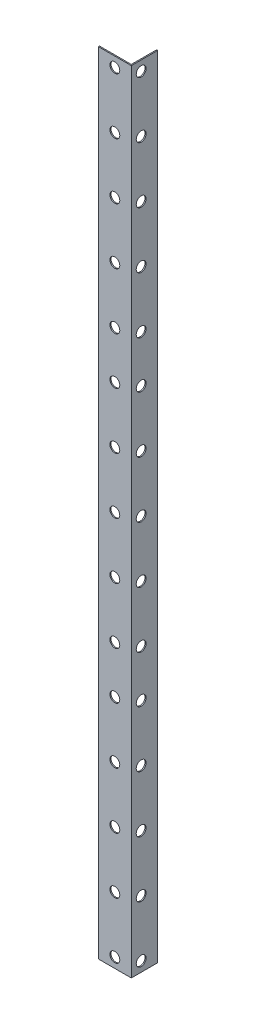
SolidWorks part; units mm, degrees
material "6061-T6 (SS)"
ref_plane "Alzado" through (0, 0, 0) normal (0, 0, 1) x (1, 0, 0)
ref_plane "Planta" through (0, 0, 0) normal (0, 1, 0) x (1, 0, 0)
ref_plane "Vista lateral" through (0, 0, 0) normal (1, 0, 0) x (0, 0, -1)
sketch "Sketch1" plane through (0, 0, 0) normal (0, 1, 0) x (1, 0, 0)
  line L0 (0, 0) -> (15, 0)
  line L1 (15, 0) -> (15, 12)
  line L2 (15, 12) -> (14.5, 12)
  line L3 (14.5, 12) -> (14.5, 0.5)
  line L4 (14.5, 0.5) -> (0, 0.5)
  line L5 (0, 0.5) -> (0, 0)
  dimension "D1" = 15
  dimension "D2" = 12
  dimension "D3" = 0.5
  dimension "D4" = 0.5
extrude "Boss-Extrude1" add sketch "Sketch1" along normal blind 360
sketch "Sketch2" plane through (14.5, 0, 0) normal (-1, 0, 0) x (0, 0, 1)
  circle A0 centre (-4.5, 355.5) radius 2.25
  circle A1 centre (-4.5, 329.8125) radius 2.25
  circle A2 centre (-4.5, 304.125) radius 2.25
  circle A3 centre (-4.5, 278.4375) radius 2.25
  circle A4 centre (-4.5, 252.75) radius 2.25
  circle A5 centre (-4.5, 231.375) radius 2.25
  circle A6 centre (-4.5, 205.6875) radius 2.25
  circle A7 centre (-4.5, 180) radius 2.25
  circle A8 centre (-4.5, 154.3125) radius 2.25
  circle A9 centre (-4.5, 128.625) radius 2.25
  circle A10 centre (-4.5, 107.25) radius 2.25
  circle A11 centre (-4.5, 81.5625) radius 2.25
  circle A12 centre (-4.5, 55.875) radius 2.25
  circle A13 centre (-4.5, 30.1875) radius 2.25
  circle A14 centre (-4.5, 4.5) radius 2.25
  dimension "D1" = 4.5
extrude "Cut-Extrude1" cut sketch "Sketch2" against normal up to next
sketch "Sketch3" plane through (0, 0, 0) normal (0, 0, 1) x (1, 0, 0)
  circle A0 centre (7.5, 355.5) radius 2.25
  circle A1 centre (7.5, 329.8437) radius 2.25
  circle A2 centre (7.5, 304.1875) radius 2.25
  circle A3 centre (7.5, 278.5312) radius 2.25
  circle A4 centre (7.5, 252.875) radius 2.25
  circle A5 centre (7.5, 231.3125) radius 2.25
  circle A6 centre (7.5, 205.6562) radius 2.25
  circle A7 centre (7.5, 180) radius 2.25
  circle A8 centre (7.5, 154.3437) radius 2.25
  circle A9 centre (7.5, 128.6875) radius 2.25
  circle A10 centre (7.5, 107.125) radius 2.25
  circle A11 centre (7.5, 81.4687) radius 2.25
  circle A12 centre (7.5, 55.8125) radius 2.25
  circle A13 centre (7.5, 30.1562) radius 2.25
  circle A14 centre (7.5, 4.5) radius 2.25
  dimension "D1" = 4.5
extrude "Cut-Extrude2" cut sketch "Sketch3" against normal up to next
